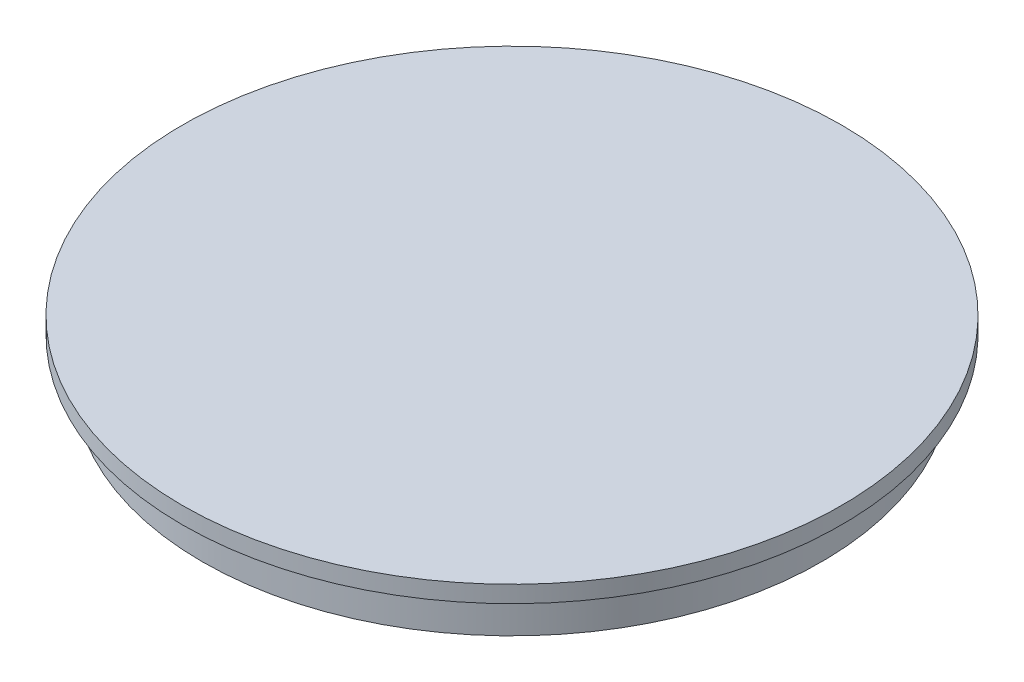
SolidWorks part; units mm, degrees
ref_plane "Front Plane" through (0, 0, 0) normal (0, 0, 1) x (1, 0, 0)
ref_plane "Top Plane" through (0, 0, 0) normal (0, 1, 0) x (1, 0, 0)
ref_plane "Right Plane" through (0, 0, 0) normal (1, 0, 0) x (0, 0, -1)
sketch "Sketch1" plane through (0, 0, 0) normal (0, 1, 0) x (1, 0, 0)
  circle A0 centre (0, 0) radius 73.75
  dimension "D1" = 147.5
extrude "Boss-Extrude1" add sketch "Sketch1" along normal blind 10
sketch "Sketch2" plane through (0, 10, 0) normal (0, 1, 0) x (1, 0, 0)
  circle A0 centre (0, 0) radius 78.5
  dimension "D1" = 157
extrude "Boss-Extrude2" add sketch "Sketch2" along normal blind 4
